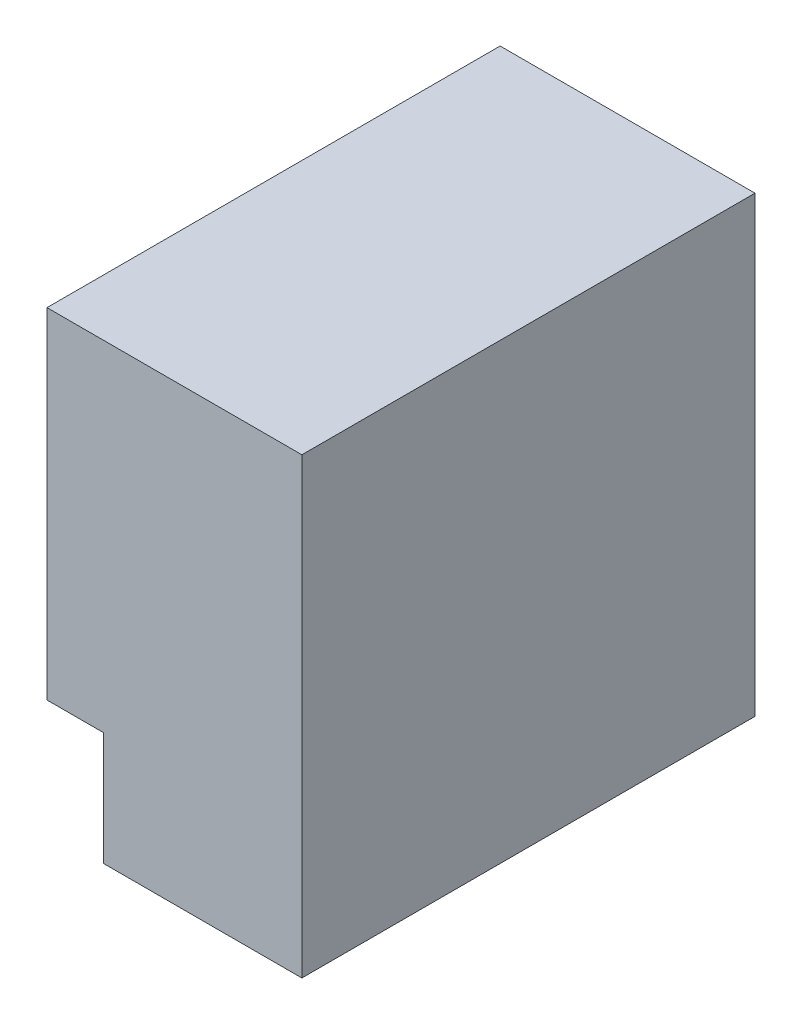
SolidWorks part; units mm, degrees
ref_plane "Front Plane" through (0, 0, 0) normal (0, 0, 1) x (1, 0, 0)
ref_plane "Top Plane" through (0, 0, 0) normal (0, 1, 0) x (1, 0, 0)
ref_plane "Right Plane" through (0, 0, 0) normal (1, 0, 0) x (0, 0, -1)
sketch "Sketch1" plane through (0, 3, 0) normal (0, 1, 0) x (-1, 0, 0)
  line L0 (34.1432, 25.1297) -> (-45.8568, 25.1297) construction
  line L1 (-5.8568, -14.8703) -> (16.6432, -14.8703)
  line L2 (-5.8568, -14.8703) -> (-5.8568, 25.1297)
  line L3 (-5.8568, 25.1297) -> (16.6432, 25.1297)
  line L4 (16.6432, -14.8703) -> (16.6432, 25.1297)
  dimension "D1" = 22.5
extrude "Boss-Extrude1" add sketch "Sketch1" along normal blind 40
sketch "Sketch2" plane through (0, 0, 25.1297) normal (0, 0, 1) x (1, 0, 0)
  line L1 (-16.6432, 3) -> (-11.6432, 3)
  line L2 (-16.6432, 3) -> (-16.6432, 13)
  line L3 (-16.6432, 13) -> (-11.6432, 13)
  line L4 (-11.6432, 3) -> (-11.6432, 13)
  dimension "D1" = 5
  dimension "D2" = 10
extrude "Cut-Extrude1" cut sketch "Sketch2" against normal blind 40
sketch "Sketch3" plane through (-16.6432, 0, 0) normal (-1, 0, 0) x (0, 0, 1)
  line L0 (5.1297, 43) -> (5.1297, 13) construction
  line L1 (-14.8703, 43) -> (25.1297, 43) construction
  line L2 (-14.8703, 13) -> (25.1297, 13) construction
hole_wizard "M3x0.5 Tapped Hole2" positions "Sketch6" profile "Sketch5" tap size "M3x0.5" standard "Ansi Metric"
sketch "Sketch6" plane through (-16.6432, 0, 0) normal (-1, 0, 0) x (0, 0, 1)
  line L0 (5.1297, 43) -> (5.1297, 13) construction
  line L1 (-14.8703, 13) -> (25.1297, 13) construction
  line L2 (-14.8703, 43) -> (25.1297, 43) construction
  point P0 (5.1297, 23)
  point P1 (5.1297, 33)
  dimension "D1" = 10
  dimension "D2" = 10
sketch "Sketch5" plane through (-16.6432, 23, 5.1297) normal (0, 1, 0) x (0, 0, 1)
  line L0 (0, 0) -> (0, 7.2511)
  line L1 (0, 7.2511) -> (1.25, 6.5)
  line L2 (1.25, 6.5) -> (1.25, 0)
  line L5 (1.25, 0) -> (0, 0)
  line L10 (0, 7.2511) -> (-1.25, 6.5) construction
  line L11 (0, -6.35) -> (0, 107.95) construction
  dimension "Tap Drill Dia." = 2.5
  dimension "Tap Drill Depth" = 6.5
  dimension "Drill Angle" = 118
cosmetic thread "Hole Thread3" parameters "D1"=4, "D2"=3
cosmetic thread "Hole Thread4" parameters "D1"=4, "D2"=3
hole_wizard "M3x0.5 Tapped Hole3" positions "Sketch8" profile "Sketch7" tap size "M3x0.5" standard "Ansi Metric"
sketch "Sketch8" plane through (0, 3, 0) normal (0, -1, 0) x (1, 0, 0)
  point P0 (-2.1432, 17.1297)
  point P1 (-2.1432, -6.8703)
sketch "Sketch7" plane through (-2.1432, 3, 17.1297) normal (1, 0, 0) x (0, 0, -1)
  line L0 (0, 0) -> (0, 7.2511)
  line L1 (0, 7.2511) -> (1.25, 6.5)
  line L2 (1.25, 6.5) -> (1.25, 0)
  line L5 (1.25, 0) -> (0, 0)
  line L10 (0, 7.2511) -> (-1.25, 6.5) construction
  line L11 (0, -6.35) -> (0, 107.95) construction
  dimension "Tap Drill Dia." = 2.5
  dimension "Tap Drill Depth" = 6.5
  dimension "Drill Angle" = 118
cosmetic thread "Hole Thread5" parameters "D1"=4, "D2"=3
cosmetic thread "Hole Thread6" parameters "D1"=4, "D2"=3
